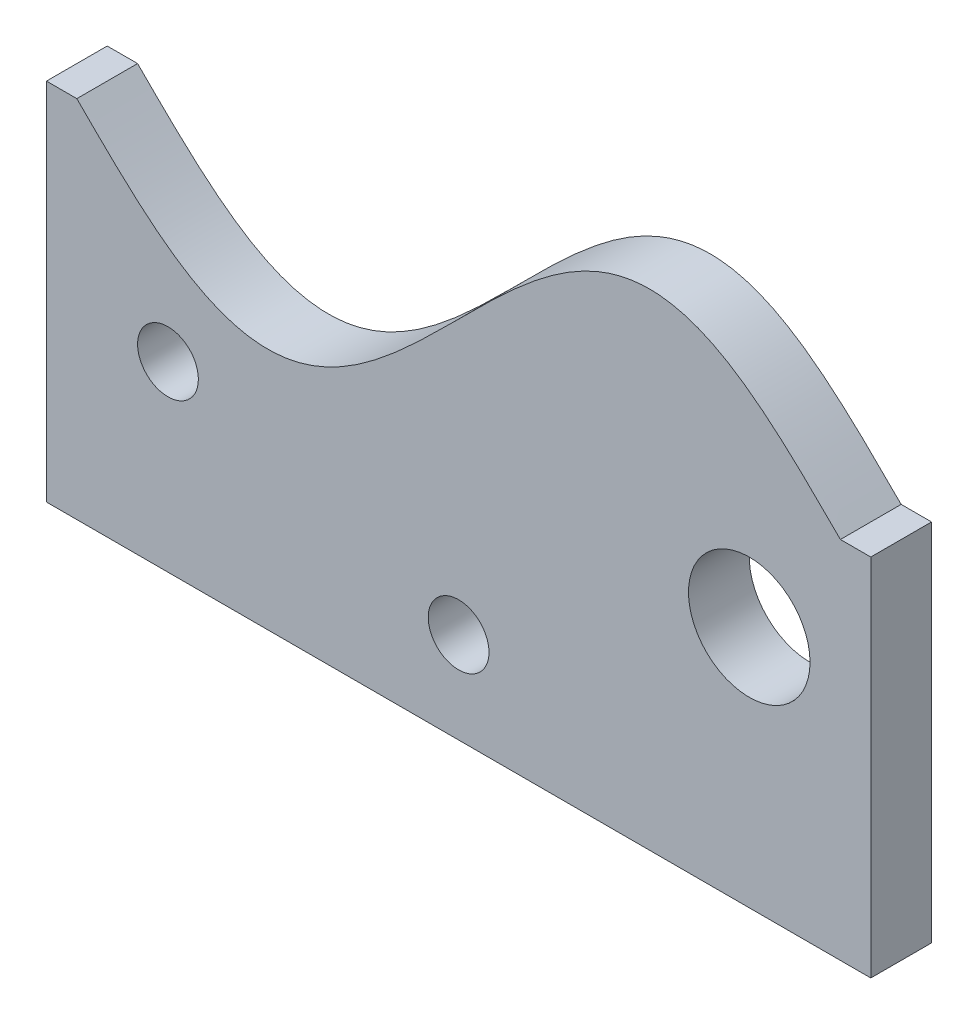
SolidWorks part; units mm, degrees
ref_plane "Front Plane" through (0, 0, 0) normal (0, 0, 1) x (1, 0, 0)
ref_plane "Top Plane" through (0, 0, 0) normal (0, 1, 0) x (1, 0, 0)
ref_plane "Right Plane" through (0, 0, 0) normal (1, 0, 0) x (0, 0, -1)
sketch "Sketch1" plane through (0, 0, 0) normal (0, 0, 1) x (1, 0, 0)
  line L0 (-79.7965, 76.2) -> (-86.1465, 76.2)
  line L1 (-86.1465, 76.2) -> (-86.1465, 0)
  line L4 (79.7965, 76.2) -> (86.1465, 76.2)
  line L5 (86.1465, 76.2) -> (86.1465, 0)
  line L6 (-86.1465, 0) -> (86.1465, 0)
  circle A0 centre (-60.7465, 38.1) radius 6.35
  circle A1 centre (0, 19.05) radius 6.35
  circle A2 centre (60.7465, 50.8) radius 12.7
  spline S0 degree 4 poles (-93.8406, 89.5395) (-93.3796, 89.147) (-92.4631, 88.3555) (-91.331, 87.3506) (-89.9894, 86.126) (-88.8814, 85.0947) (-88.0003, 84.264) (-87.1248, 83.4289) (-86.2481, 82.584) (-85.5029, 81.8598) (-84.8385, 81.2094) (-84.2722, 80.6524) (-83.8445, 80.2308) (-82.9421, 79.342) (-80.1826, 76.5887) (-79.6581, 76.0593) (-76.8399, 73.2464) (-75.851, 72.2705) (-75.0347, 71.465) (-74.3114, 70.7565) (-73.576, 70.0405) (-72.6491, 69.1444) (-71.5323, 68.0766) (-70.2195, 66.8415) (-68.4855, 65.2479) (-66.8077, 63.7566) (-65.1853, 62.3691) (-63.619, 61.0865) (-62.3477, 60.083) (-60.7337, 58.8607) (-58.9999, 57.6267) (-57.1349, 56.4004) (-54.6898, 54.9494) (-51.6614, 53.3831) (-47.6814, 51.7986) (-42.7562, 50.7248) (-37.484, 50.6974) (-31.9632, 51.8001) (-26.9589, 53.8398) (-22.3741, 56.4855) (-17.5555, 59.906) (-12.8998, 63.7459) (-7.9384, 68.3175) (-2.6275, 73.554) (2.6275, 78.846) (7.9384, 84.0826) (12.8998, 88.6541) (17.5555, 92.494) (22.3741, 95.9145) (26.9589, 98.5603) (31.9633, 100.5998) (37.4839, 101.7027) (42.7563, 101.6751) (47.6812, 100.6015) (52.1353, 98.8282) (55.851, 96.8244) (58.9271, 94.8484) (61.7164, 92.8275) (64.261, 90.8137) (66.8932, 88.5842) (69.2599, 86.455) (71.3353, 84.5163) (73.2269, 82.7005) (74.6406, 81.325) (76.2276, 79.7588) (77.4656, 78.5297) (79.4276, 76.5693) (80.3595, 75.6364) (82.5914, 73.407) (83.9523, 72.0604) (85.8962, 70.1506) (87.5083, 68.6009) (89.3545, 66.8541) (90.8615, 65.4752) (92.247, 64.2351) (93.1481, 63.4533) (93.6089, 63.058) (93.841, 62.8602) knots 0 0 0 0 0 0.010403 0.020805 0.026006 0.031208 0.036409 0.04161 0.046811 0.052013 0.054613 0.057214 0.059814 0.062415 0.08322 0.100918 0.105342 0.109767 0.114191 0.118615 0.12304 0.127464 0.136313 0.145162 0.154011 0.167923 0.174879 0.181836 0.188792 0.195748 0.209661 0.218392 0.227124 0.244588 0.268185 0.291782 0.313137 0.334493 0.364357 0.384128 0.403899 0.435933 0.467966 0.5 0.532034 0.564067 0.596101 0.615872 0.635643 0.665507 0.686863 0.708218 0.731815 0.755412 0.772876 0.790339 0.804252 0.818164 0.832077 0.845989 0.863687 0.872536 0.881385 0.890233 0.899082 0.907931 0.91678 0.927182 0.937585 0.947987 0.95839 0.968792 0.979195 0.989597 0.994799 1 1 1 1 1 construction
  spline S1 degree 4 poles (-79.7965, 76.2) (-79.1893, 75.5929) (-78.4198, 74.8234) (-76.8399, 73.2464) (-75.851, 72.2705) (-75.0347, 71.465) (-74.3114, 70.7565) (-73.576, 70.0405) (-72.6491, 69.1444) (-71.5323, 68.0766) (-70.2195, 66.8415) (-68.4855, 65.2479) (-66.8077, 63.7566) (-65.1853, 62.3691) (-63.619, 61.0865) (-62.3477, 60.083) (-60.7337, 58.8607) (-58.9999, 57.6267) (-57.1349, 56.4004) (-54.6898, 54.9494) (-51.6614, 53.3831) (-47.6814, 51.7986) (-42.7562, 50.7248) (-37.484, 50.6974) (-31.9632, 51.8001) (-26.9589, 53.8398) (-22.3741, 56.4855) (-17.5555, 59.906) (-12.8998, 63.7459) (-7.9384, 68.3175) (-2.6275, 73.554) (2.6275, 78.846) (7.9384, 84.0826) (12.8998, 88.6541) (17.5555, 92.494) (22.3741, 95.9145) (26.9589, 98.5603) (31.9633, 100.5998) (37.4839, 101.7027) (42.7563, 101.6751) (47.6812, 100.6015) (52.1353, 98.8282) (55.851, 96.8244) (58.9271, 94.8484) (61.7164, 92.8275) (64.261, 90.8137) (66.8932, 88.5842) (69.2599, 86.455) (71.3353, 84.5163) (73.2269, 82.7005) (74.6406, 81.325) (76.2276, 79.7588) (77.4656, 78.5297) (78.8752, 77.1212) (79.4929, 76.5036) (79.7965, 76.2) knots 0.08322 0.08322 0.08322 0.08322 0.08322 0.100918 0.105342 0.109767 0.114191 0.118615 0.12304 0.127464 0.136313 0.145162 0.154011 0.167923 0.174879 0.181836 0.188792 0.195748 0.209661 0.218392 0.227124 0.244588 0.268185 0.291782 0.313137 0.334493 0.364357 0.384128 0.403899 0.435933 0.467966 0.5 0.532034 0.564067 0.596101 0.615872 0.635643 0.665507 0.686863 0.708218 0.731815 0.755412 0.772876 0.790339 0.804252 0.818164 0.832077 0.845989 0.863687 0.872536 0.881385 0.890233 0.899082 0.907931 0.91678 0.91678 0.91678 0.91678 0.91678
  point P7 (0, 0)
  point P16 (0, 0)
  dimension "D5" = 25.4
  dimension "D6" = 12.7
  dimension "D7" = 38.1
  dimension "D1" = 6.35
  dimension "D2" = 6.35
  dimension "D3" = 76.2
  dimension "D4" = 76.2
  dimension "D8" = 25.4
  dimension "D9" = 19.05
  dimension "D10" = 25.4
  dimension "D11" = 50.8
extrude "Boss-Extrude1" add sketch "Sketch1" along normal mid plane 12.7
